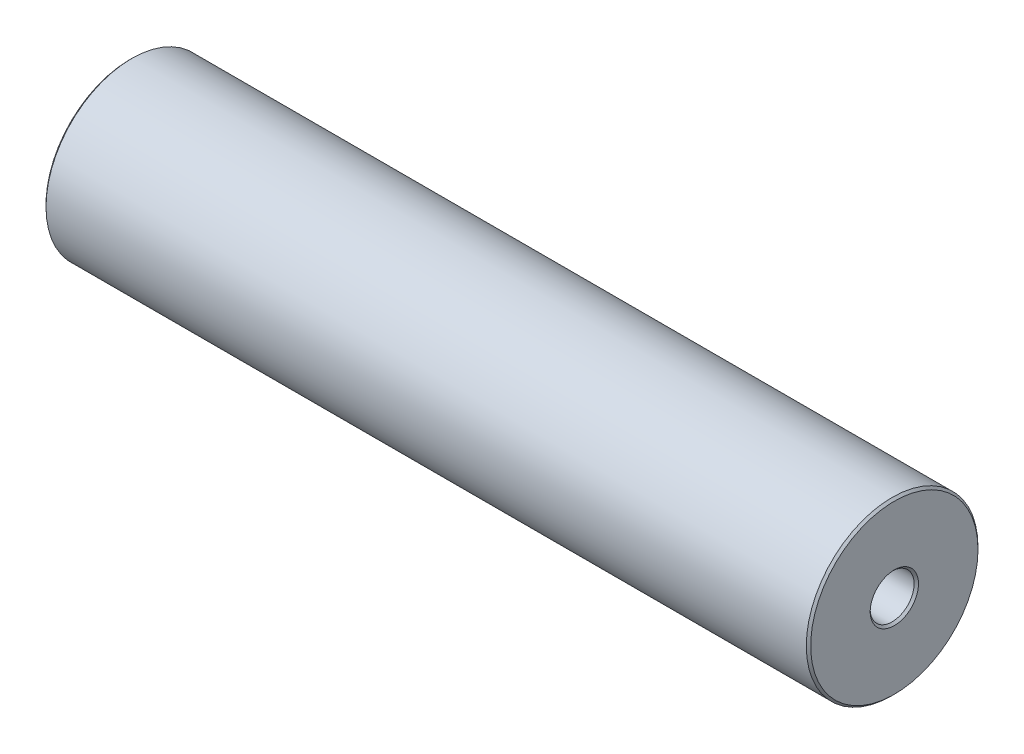
SolidWorks part; units mm, degrees
material "6061-T6 (SS)"
ref_plane "Front Plane" through (0, 0, 0) normal (0, 0, 1) x (1, 0, 0)
ref_plane "Top Plane" through (0, 0, 0) normal (0, 1, 0) x (1, 0, 0)
ref_plane "Right Plane" through (0, 0, 0) normal (1, 0, 0) x (0, 0, -1)
sketch "Sketch2" plane through (0, 0, 0) normal (1, 0, 0) x (0, 0, -1)
  circle A0 centre (0, 0) radius 9.9809
  dimension "D1" = 19.9619
extrude "Boss-Extrude1" add sketch "Sketch2" along normal mid plane 88.9
hole_wizard "1/4-20 Tapped Hole1" positions "3DSketch1" profile "Sketch3" tap size "1/4-20" standard "ANSI Inch"
sketch3d "3DSketch1"
  line L0 (44.45, 0, 0) -> (-44.45, 0, 0) construction
  point P53 (14.9561, -44.6578, 0)
  point P56 (44.45, 0, 0)
  point P60 (-44.45, 0, 0)
sketch "Sketch3" plane through (-44.45, 0, 0) normal (0, 1, 0) x (0, 0, 1)
  line L0 (0, 0) -> (0, 18.0438)
  line L1 (0, 18.0438) -> (2.5527, 16.51)
  line L2 (2.5527, 16.51) -> (2.5527, 0)
  line L5 (2.5527, 0) -> (0, 0)
  line L10 (0, 18.0438) -> (-2.5527, 16.51) construction
  line L11 (0, -6.35) -> (0, 107.95) construction
  dimension "Tap Drill Dia." = 5.1054
  dimension "Tap Drill Depth" = 16.51
  dimension "Drill Angle" = 118
cosmetic thread "Hole Thread1" parameters "D1"=12.7, "D2"=6.35
cosmetic thread "Hole Thread2" parameters "D1"=12.7, "D2"=6.35
cosmetic thread "Hole Thread3" parameters "D1"=12.7, "D2"=6.35
chamfer "Chamfer1" distance 0.254 angle 45 4 edges at (44.45, 0, -9.9809) (-44.45, 0, -9.9809) (44.45, 0, -2.5527) (-44.45, 0, 2.5527)
equation "\"D1@Sketch2\"=20mm-0.0015"
